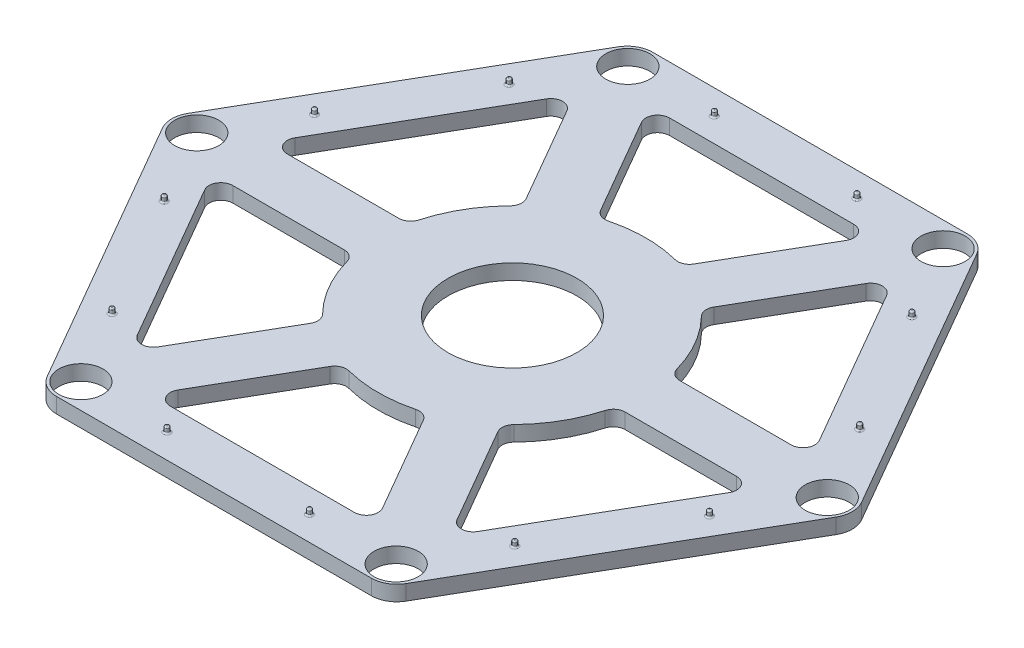
SolidWorks part; units mm, degrees
ref_plane "Front Plane" through (0, 0, 0) normal (0, 0, 1) x (1, 0, 0)
ref_plane "Top Plane" through (0, 0, 0) normal (0, 1, 0) x (1, 0, 0)
ref_plane "Right Plane" through (0, 0, 0) normal (1, 0, 0) x (0, 0, -1)
sketch "Sketch1" plane through (0, 0, 0) normal (0, 1, 0) x (1, 0, 0)
  line L1 (-20.3, 35.1606) -> (-40.6, 0)
  line L2 (-40.6, 0) -> (-20.3, -35.1606)
  line L3 (-20.3, -35.1606) -> (20.3, -35.1606)
  line L4 (20.3, -35.1606) -> (40.6, 0)
  line L5 (40.6, 0) -> (20.3, 35.1606)
  line L6 (20.3, 35.1606) -> (-20.3, 35.1606)
  line L7 (-17, 29.4449) -> (-34, 0)
  line L8 (-34, 0) -> (-17, -29.4449)
  line L9 (-17, -29.4449) -> (17, -29.4449)
  line L10 (17, -29.4449) -> (34, 0)
  line L11 (34, 0) -> (17, 29.4449)
  line L12 (17, 29.4449) -> (-17, 29.4449)
  line L13 (-18.6638, 32.2165) -> (-37.3656, -0.0563) construction
  line L14 (-37.3656, -0.0563) -> (-18.7674, -32.3889) construction
  line L15 (-18.7674, -32.3889) -> (18.5325, -32.4487) construction
  line L16 (18.5325, -32.4487) -> (37.3, 0) construction
  line L17 (37.3, 0) -> (18.6362, 32.2165) construction
  line L18 (18.6362, 32.2165) -> (-18.6638, 32.2165) construction
  line L50 (-17, 29.4449) -> (17, -29.4449) construction
  line L51 (-17, 29.4449) -> (-18.8579, 26.2268)
  line L56 (-13.2841, 29.4449) -> (-17, 29.4449)
  line L57 (-13.3543, 16.6943) -> (-7.7805, 19.9123) construction
  line L58 (-17, 29.4449) -> (-13.2841, 29.4449)
  line L59 (-13.2841, 29.4449) -> (-4.9475, 15.0054)
  line L60 (-17, 29.4449) -> (-18.8579, 26.2268)
  line L61 (-18.8579, 26.2268) -> (-10.5213, 11.7874)
  line L62 (17, 29.4449) -> (13.2841, 29.4449)
  line L63 (13.2841, 29.4449) -> (4.9475, 15.0054)
  line L66 (18.8579, 26.2268) -> (10.5213, 11.7874)
  line L67 (17, 29.4449) -> (18.8579, 26.2268)
  line L68 (34, 0) -> (32.1421, 3.2181)
  line L69 (32.1421, 3.2181) -> (15.4688, 3.2181)
  line L72 (32.1421, -3.2181) -> (15.4688, -3.2181)
  line L73 (34, 0) -> (32.1421, -3.2181)
  line L74 (17, -29.4449) -> (18.8579, -26.2268)
  line L75 (18.8579, -26.2268) -> (10.5213, -11.7874)
  line L78 (13.2841, -29.4449) -> (4.9475, -15.0054)
  line L79 (17, -29.4449) -> (13.2841, -29.4449)
  line L80 (-17, -29.4449) -> (-13.2841, -29.4449)
  line L81 (-13.2841, -29.4449) -> (-4.9475, -15.0054)
  line L84 (-18.8579, -26.2268) -> (-10.5213, -11.7874)
  line L85 (-17, -29.4449) -> (-18.8579, -26.2268)
  line L86 (-34, 0) -> (-32.1421, -3.2181)
  line L87 (-32.1421, -3.2181) -> (-15.4688, -3.2181)
  line L90 (-32.1421, 3.2181) -> (-15.4688, 3.2181)
  line L91 (-34, 0) -> (-32.1421, 3.2181)
  line L92 (18.6362, 32.2165) -> (31.4889, 27.5601) construction
  circle A0 centre (0.0529, 0) radius 7.6
  circle A2 centre (0.0529, 0) radius 11.5 construction
  arc A4 (-10.5213, 11.7874) -> (-15.4688, 3.2181) centre (0, 0) ccw
  arc A5 (4.9475, 15.0054) -> (-4.9475, 15.0054) centre (0, 0) ccw
  arc A6 (15.4688, 3.2181) -> (10.5213, 11.7874) centre (0, 0) ccw
  arc A7 (10.5213, -11.7874) -> (15.4688, -3.2181) centre (0, 0) ccw
  arc A8 (-4.9475, -15.0054) -> (4.9475, -15.0054) centre (0, 0) ccw
  arc A9 (-15.4688, -3.2181) -> (-10.5213, -11.7874) centre (0, 0) ccw
  circle A16 centre (18.6362, 32.2165) radius 2.6
  circle A17 centre (37.2184, -0.0312) radius 2.6
  circle A18 centre (18.5822, -32.2477) radius 2.6
  circle A19 centre (-18.6362, -32.2165) radius 2.6
  circle A20 centre (-37.2184, 0.0312) radius 2.6
  circle A21 centre (-18.5822, 32.2477) radius 2.6
  point P40 (0, 0)
  point P42 (0, 0)
  point P58 (0.0529, 0)
  point P59 (0, 0)
  point P62 (0, 0)
  point P77 (0, 0)
  point P82 (0, 0)
  point P92 (0, 0)
  dimension "D7" = 6
  dimension "D5" = 40
  dimension "D6" = 5.2
  dimension "D1" = 40.6
  dimension "D2" = 6.6
  dimension "D3" = 3.3
  dimension "D4" = 6
extrude "Boss-Extrude1" add sketch "Sketch1" along normal blind 1.8
fillet "Fillet1" radius 3 6 edges at (-40.6, 0.9, 0) (-20.3, 0.9, 35.1606) (20.3, 0.9, 35.1606) (40.6, 0.9, 0) (20.3, 0.9, -35.1606) (-20.3, 0.9, -35.1606)
fillet "Fillet2" radius 1.4 24 edges at (-32.1421, 0.9, 3.2181) (-15.4688, 0.9, 3.2181) (-10.5213, 0.9, 11.7874) (-18.8579, 0.9, 26.2268) (-13.2841, 0.9, 29.4449) (13.2841, 0.9, 29.4449) (-4.9475, 0.9, 15.0054) (4.9475, 0.9, 15.0054) (18.8579, 0.9, 26.2268) (10.5213, 0.9, 11.7874) (15.4688, 0.9, 3.2181) (32.1421, 0.9, 3.2181) (32.1421, 0.9, -3.2181) (18.8579, 0.9, -26.2268) (15.4688, 0.9, -3.2181) (10.5213, 0.9, -11.7874) (-32.1421, 0.9, -3.2181) (-15.4688, 0.9, -3.2181) (-4.9475, 0.9, -15.0054) (-13.2841, 0.9, -29.4449) (4.9475, 0.9, -15.0054) (13.2841, 0.9, -29.4449) (-10.5213, 0.9, -11.7874) (-18.8579, 0.9, -26.2268)
ref_plane "Plane1" through (0, 1.8, 0) normal (0, 1, 0) x (1, 0, 0)
scale "Scale1" scale about centroid uniform scaling yes scale factor 1.15
sketch "Sketch4" plane through (0, 1.935, 0) normal (0, 1, 0) x (1, 0, 0)
  line L0 (0, 0) -> (0, 58.4234) construction
  circle A0 centre (-9.6664, 37.1251) radius 0.3
  circle A1 centre (9.6664, 37.1251) radius 0.3
  circle A2 centre (27.3181, 26.9339) radius 0.3
  circle A3 centre (36.9845, 10.1913) radius 0.3
  circle A4 centre (36.9845, -10.1913) radius 0.3
  circle A5 centre (27.3181, -26.9339) radius 0.3
  circle A6 centre (9.6664, -37.1251) radius 0.3
  circle A7 centre (-9.6664, -37.1251) radius 0.3
  circle A8 centre (-27.3181, -26.9339) radius 0.3
  circle A9 centre (-36.9845, -10.1913) radius 0.3
  circle A10 centre (-36.9845, 10.1913) radius 0.3
  circle A11 centre (-27.3181, 26.9339) radius 0.3
  dimension "D1" = 6
extrude "Boss-Extrude3" add sketch "Sketch4" along normal blind 0.8
fillet "Fillet5" radius 0.2 24 edges at (27.3181, 1.935, -26.6339) (27.3181, 2.735, -26.6339) (36.9845, 1.935, -10.4913) (36.9845, 2.735, -10.4913) (36.9845, 1.935, 10.4913) (36.9845, 2.735, 10.4913) (27.3181, 1.935, 26.6339) (27.3181, 2.735, 26.6339) (9.6664, 1.935, 37.4251) (9.6664, 2.735, 37.4251) (-9.6664, 1.935, 36.8251) (-9.6664, 2.735, 36.8251) (-27.3181, 1.935, 27.2339) (-27.3181, 2.735, 27.2339) (-36.9845, 1.935, 9.8913) (-36.9845, 2.735, 9.8913) (-36.9845, 1.935, -9.8913) (-36.9845, 2.735, -9.8913) (-27.3181, 1.935, -27.2339) (-27.3181, 2.735, -27.2339) (9.6664, 1.935, -37.4251) (-9.6664, 1.935, -36.8251) (9.6664, 2.735, -37.4251) (-9.6664, 2.735, -36.8251)
